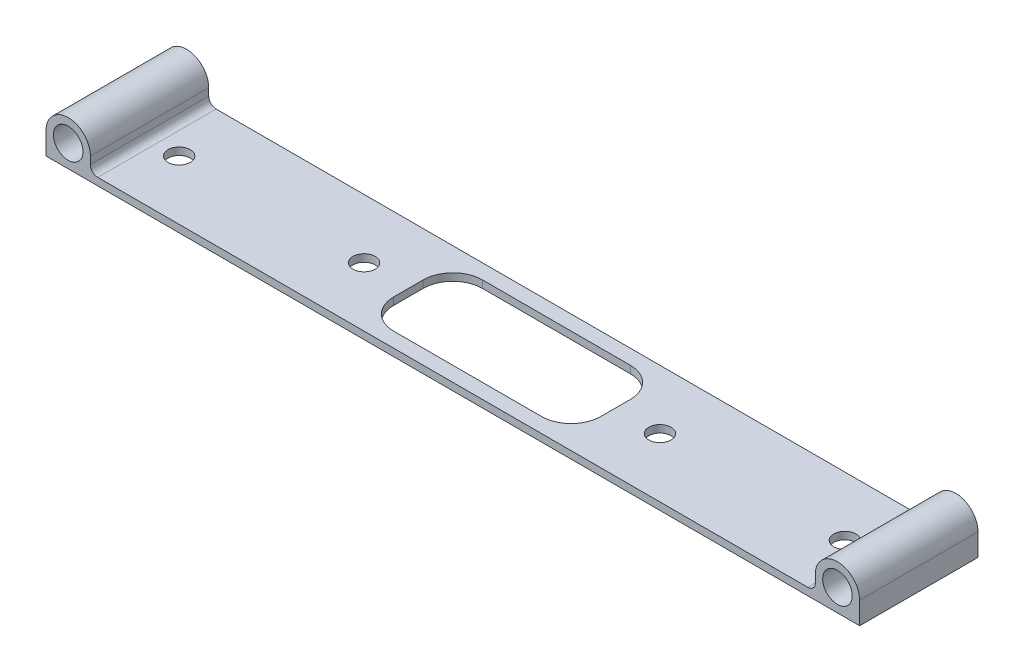
SolidWorks part; units mm, degrees
material "6061-T6 (SS)"
ref_plane "Front Plane" through (0, 0, 0) normal (0, 0, 1) x (1, 0, 0)
ref_plane "Top Plane" through (0, 0, 0) normal (0, 1, 0) x (1, 0, 0)
ref_plane "Right Plane" through (0, 0, 0) normal (1, 0, 0) x (0, 0, -1)
sketch "Sketch1" plane through (0, 0, 0) normal (0, 0, 1) x (1, 0, 0)
  line L0 (-6.35, 0) -> (-6.35, -6.35)
  line L1 (6.35, 0) -> (6.35, -6.35)
  line L2 (-6.35, -6.35) -> (-9.525, -6.35)
  line L3 (6.35, -6.35) -> (9.525, -6.35)
  line L4 (-9.525, -6.35) -> (-9.525, -9.525)
  line L5 (-9.525, -9.525) -> (9.525, -9.525)
  line L6 (-9.525, 0) -> (-9.525, -6.35)
  line L7 (9.525, 0) -> (9.525, -6.35)
  line L8 (9.525, -6.35) -> (165.1, -6.35)
  line L9 (165.1, -6.35) -> (165.1, -9.525)
  line L10 (9.525, -9.525) -> (9.525, -6.35)
  line L11 (-6.35, -6.35) -> (6.35, -6.35)
  line L12 (165.1, -9.525) -> (9.525, -9.525)
  circle A0 centre (0, 0) radius 6.35
  arc A1 (-9.525, 0) -> (9.525, 0) centre (0, 0) cw
  dimension "D1" = 12.7
  dimension "D6" = 3.175
  dimension "D2" = 165.1
  dimension "D3" = 3.175
  dimension "D7" = 3.175
  dimension "D8" = 3.175
extrude "Boss-Extrude1" add sketch "Sketch1" along normal blind 50.8
sketch "Sketch6" plane through (0, -6.35, 0) normal (0, 1, 0) x (1, 0, 0)
  line L0 (165.1, -25.4) -> (9.3644, -25.4) construction
  line L4 (9.525, -50.8) -> (9.525, 0) construction
  line L5 (165.1, -50.8) -> (165.1, 0) construction
  circle A0 centre (22.225, -25.4) radius 4.7625
  circle A1 centre (101.6, -25.4) radius 4.7625
  dimension "D1" = 9.525
  dimension "D2" = 9.525
  dimension "D3" = 12.7
  dimension "D4" = 79.375
extrude "Cut-Extrude3" cut sketch "Sketch6" against normal blind 12.7
mirror "Mirror1" about plane through (165.1, 0, 50.8) normal (1, 0, 0) of "Cut-Extrude3", "Boss-Extrude1"
sketch "Sketch7" plane through (0, -6.35, 0) normal (0, 1, 0) x (1, 0, 0)
  line L0 (9.525, 0) -> (320.675, 0)
  line L1 (9.525, -50.8) -> (320.675, -50.8)
  line L2 (120.65, 0) -> (120.65, -50.8)
  line L3 (209.55, 0) -> (209.55, -50.8)
  line L8 (120.65, -6.35) -> (209.55, -6.35)
  line L9 (120.65, -44.45) -> (209.55, -44.45)
  line L11 (9.525, -44.45) -> (320.675, -44.45) construction
  line L12 (9.525, -6.35) -> (320.675, -6.35) construction
  circle A0 centre (101.6, -25.4) radius 4.7625 construction
  circle A1 centre (228.6, -25.4) radius 4.7625 construction
  dimension "D1" = 19.05
  dimension "D2" = 19.05
  dimension "D3" = 6.35
  dimension "D4" = 6.35
extrude "Cut-Extrude4" cut sketch "Sketch7" against normal through all contours L2 L9 L3 L8
fillet "Fillet1" radius 12.7 4 edges at (209.55, -7.9375, 6.35) (209.55, -7.9375, 44.45) (120.65, -7.9375, 44.45) (120.65, -7.9375, 6.35)
fillet "Fillet2" radius 3.175 2 edges at (9.525, -6.35, 25.4) (320.675, -6.35, 25.4)
